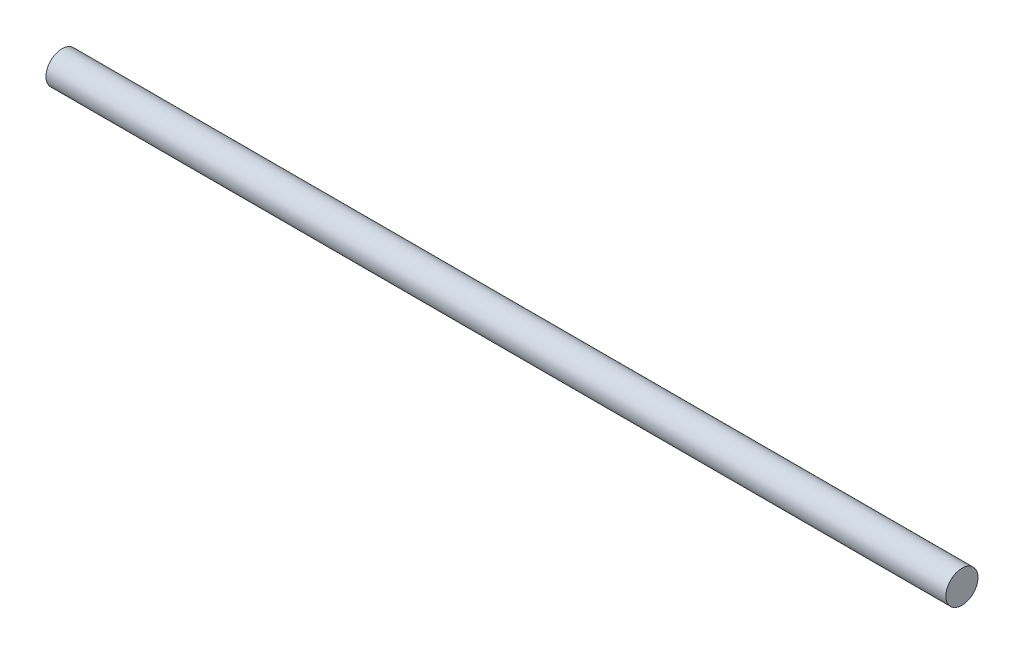
SolidWorks part; units mm, degrees
material "Plain Carbon Steel"
ref_plane "Front Plane" through (0, 0, 0) normal (0, 0, 1) x (1, 0, 0)
ref_plane "Top Plane" through (0, 0, 0) normal (0, 1, 0) x (1, 0, 0)
ref_plane "Right Plane" through (0, 0, 0) normal (1, 0, 0) x (0, 0, -1)
sketch "Sketch1" plane through (0, 0, 0) normal (1, 0, 0) x (0, 0, -1)
  circle A0 centre (0, 0) radius 3.175
  dimension "D1" = 6.35
extrude "Boss-Extrude1" add sketch "Sketch1" along normal blind 177.8
